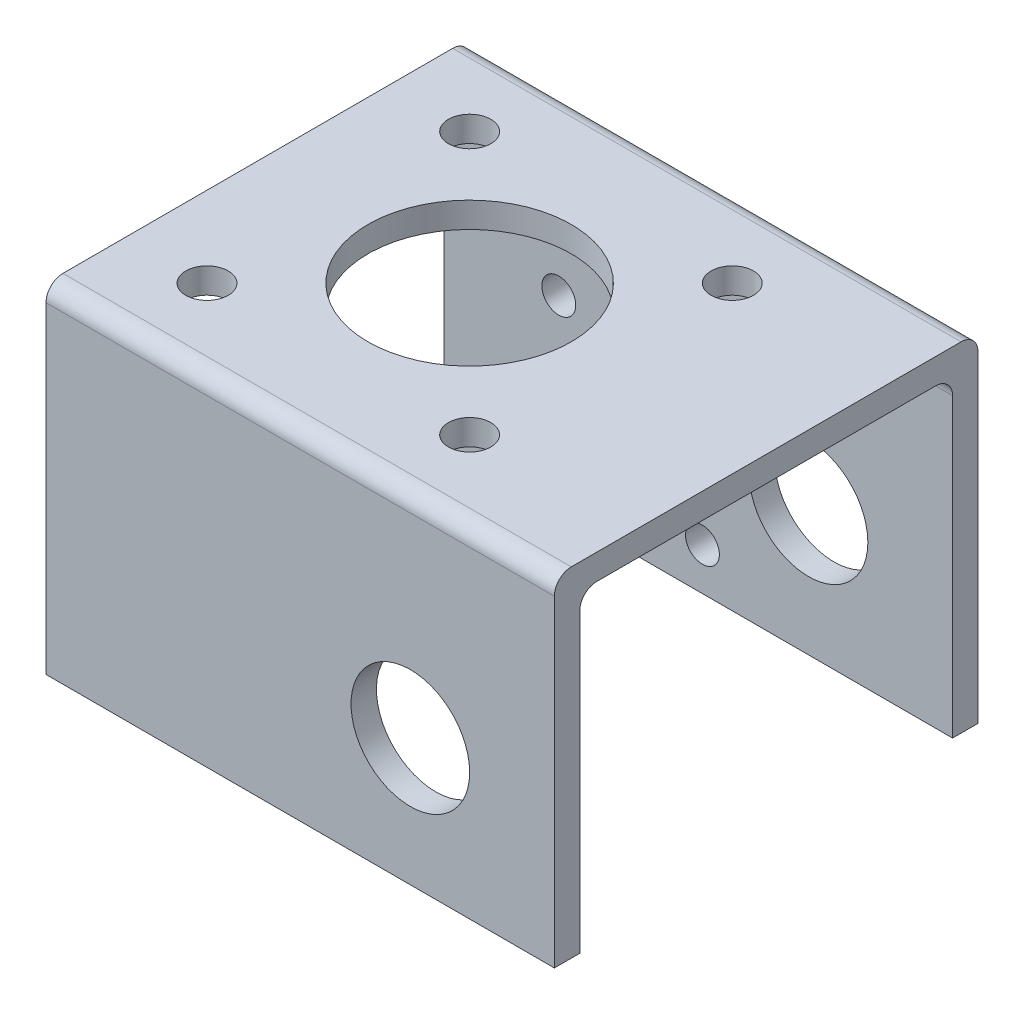
SolidWorks part; units mm, degrees
material "6061 合金"
ref_plane "前视基准面" through (0, 0, 0) normal (0, 0, 1) x (1, 0, 0)
ref_plane "上视基准面" through (0, 0, 0) normal (0, 1, 0) x (1, 0, 0)
ref_plane "右视基准面" through (0, 0, 0) normal (1, 0, 0) x (0, 0, -1)
sketch "草图1" plane through (0, 0, 0) normal (1, 0, 0) x (0, 0, -1)
  line L0 (0, 0) -> (3, 0)
  line L1 (3, 0) -> (3, 35)
  line L2 (5, 37) -> (45, 37)
  line L3 (47, 35) -> (47, 0)
  line L4 (47, 0) -> (50, 0)
  line L5 (50, 0) -> (50, 38)
  line L6 (48, 40) -> (2, 40)
  line L7 (0, 38) -> (0, 0)
  arc A0 (50, 38) -> (48, 40) centre (48, 38) ccw
  arc A1 (45, 37) -> (47, 35) centre (45, 35) cw
  arc A2 (3, 35) -> (5, 37) centre (5, 35) cw
  arc A3 (2, 40) -> (0, 38) centre (2, 38) ccw
  point P11 (50, 40)
  point P18 (0, 40)
  dimension "D6" = 2
  dimension "D1" = 3
  dimension "D2" = 3
  dimension "D3" = 3
  dimension "D4" = 50
  dimension "D5" = 40
extrude "凸台-拉伸1" add sketch "草图1" along normal blind 60
sketch "草图2" plane through (0, 40, 0) normal (0, 1, 0) x (1, 0, 0)
  line L0 (25, -19.2967) -> (25, 88.9945) construction
  line L1 (-21.8978, 25) -> (76.0197, 25) construction
  line L2 (60, 0) -> (0, 0) construction
  line L3 (0, 48) -> (0, 2) construction
  line L4 (-9.4226, 9.5) -> (65.353, 9.5) construction
  line L5 (9.5, -18.3438) -> (9.5, 73.6232) construction
  circle A0 centre (9.5, 9.5) radius 2.5
  circle A1 centre (40.5, 9.5) radius 2.5
  circle A2 centre (40.5, 40.5) radius 2.5
  circle A3 centre (9.5, 40.5) radius 2.5
  circle A4 centre (25, 25) radius 12
  dimension "D5" = 5
  dimension "D8" = 24
  dimension "D1" = 25
  dimension "D2" = 25
  dimension "D3" = 15.5
  dimension "D4" = 15.5
  dimension "D6" = 2
  dimension "D7" = 2
extrude "切除-拉伸1" cut sketch "草图2" against normal up to next
sketch "草图3" plane through (0, 0, 0) normal (0, 0, 1) x (1, 0, 0)
  line L0 (25, -15.1885) -> (25, 47.9229) construction
  line L1 (0, 38) -> (0, 0) construction
  line L2 (60, 40) -> (0, 40) construction
  circle A0 centre (43, 15) radius 7
  dimension "D1" = 14
  dimension "D2" = 25
  dimension "D3" = 18
  dimension "D4" = 25
extrude "切除-拉伸2" cut sketch "草图3" against normal through all
sketch "草图6" plane through (0, 0, -50) normal (0, 0, -1) x (-1, 0, 0)
  line L0 (-22, 38) -> (-22, -10.7821) construction
  line L1 (-60, 38) -> (0, 38) construction
  line L2 (-60, 0) -> (0, 0) construction
  line L3 (0, 0) -> (0, 38) construction
  line L4 (-22, 13.4956) -> (4.0591, 13.4956) construction
  circle A1 centre (-13.525, 5) radius 2
  circle A2 centre (-30.475, 5) radius 2
  circle A3 centre (-30.475, 21.9911) radius 2
  circle A4 centre (-13.525, 21.9911) radius 2
  circle A5 centre (-22, 13.4956) radius 12 construction
  dimension "D2" = 4
  dimension "D1" = 24
  dimension "D3" = 5
  dimension "D4" = 22
extrude "切除-拉伸3" cut sketch "草图6" against normal up to next
